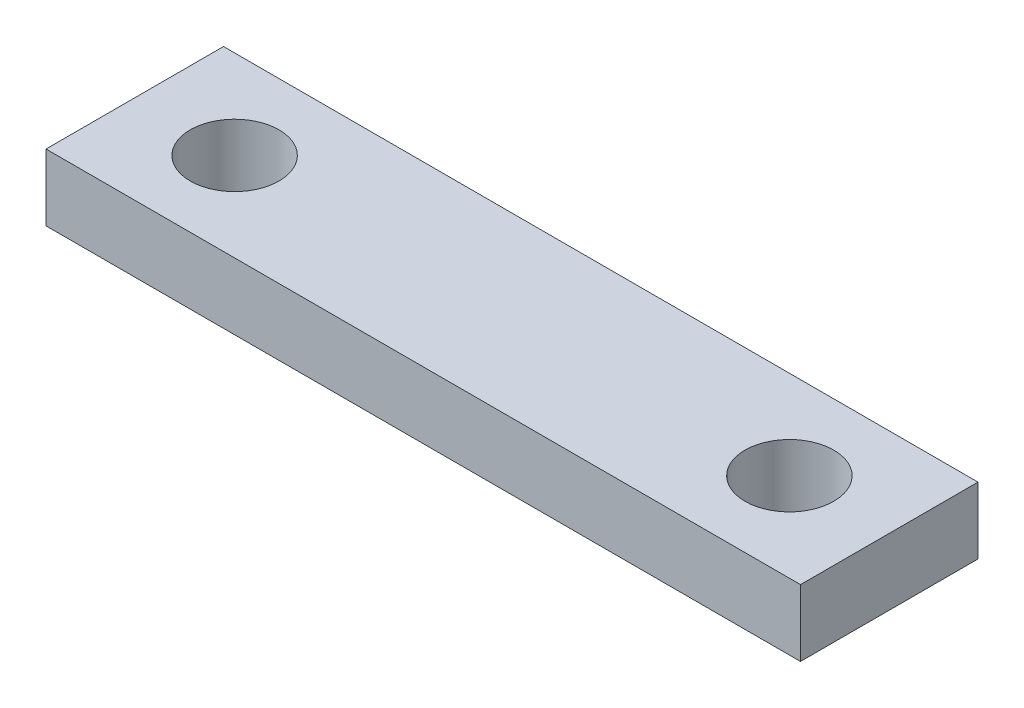
SolidWorks part; units mm, degrees
ref_plane "Front Plane" through (0, 0, 0) normal (0, 0, 1) x (1, 0, 0)
ref_plane "Top Plane" through (0, 0, 0) normal (0, 1, 0) x (1, 0, 0)
ref_plane "Right Plane" through (0, 0, 0) normal (1, 0, 0) x (0, 0, -1)
sketch "Sketch1" plane through (0, 0, 0) normal (0, 1, 0) x (1, 0, 0)
  line L0 (-12.5, 0) -> (12.5, 0) construction
  line L1 (-17, -4) -> (17, -4)
  line L2 (-17, -4) -> (-17, 4)
  line L3 (-17, 4) -> (17, 4)
  line L4 (17, -4) -> (17, 4)
  line L5 (-17, -4) -> (17, 4) construction
  line L6 (-17, 4) -> (17, -4) construction
  circle A0 centre (-12.5, 0) radius 2
  circle A1 centre (12.5, 0) radius 2
  point P0 (0, 0)
  dimension "D3" = 25
  dimension "D4" = 4
  dimension "D1" = 8
  dimension "D2" = 34
extrude "Boss-Extrude1" add sketch "Sketch1" along normal blind 3
